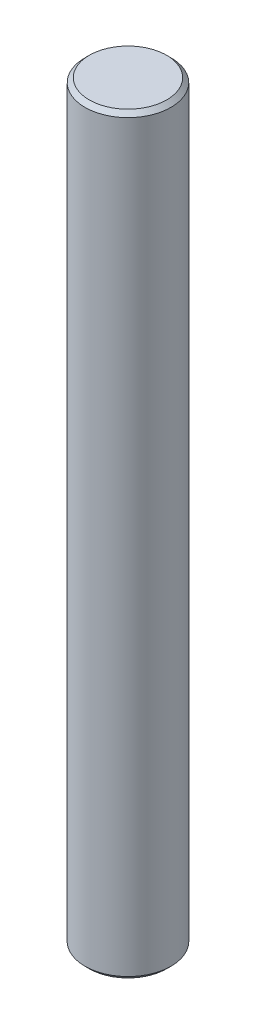
SolidWorks part; units mm, degrees
material "普通碳钢"
ref_plane "前视基准面" through (0, 0, 0) normal (0, 0, 1) x (1, 0, 0)
ref_plane "上视基准面" through (0, 0, 0) normal (0, 1, 0) x (1, 0, 0)
ref_plane "右视基准面" through (0, 0, 0) normal (1, 0, 0) x (0, 0, -1)
sketch "草图1" plane through (0, 0, 0) normal (0, 1, 0) x (1, 0, 0)
  circle A0 centre (0, 0) radius 2
  dimension "D1" = 4
extrude "凸台-拉伸1" add sketch "草图1" along normal blind 35
chamfer "倒角1" distance 0.2 angle 45 2 edges at (0, 35, 2) (0, 0, 2)
